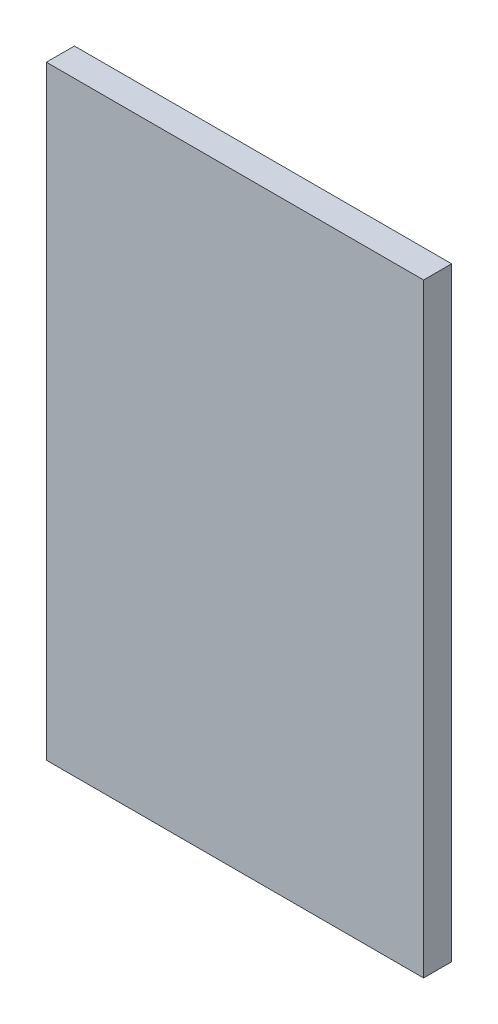
SolidWorks part; units mm, degrees
ref_plane "Front Plane" through (0, 0, 0) normal (0, 0, 1) x (1, 0, 0)
ref_plane "Top Plane" through (0, 0, 0) normal (0, 1, 0) x (1, 0, 0)
ref_plane "Right Plane" through (0, 0, 0) normal (1, 0, 0) x (0, 0, -1)
sketch "Sketch1" plane through (0, 0, 0) normal (0, 0, 1) x (1, 0, 0)
  line L0 (-39, -62.5) -> (39, 62.5) construction
  line L1 (-39, -62.5) -> (39, -62.5)
  line L2 (-39, -62.5) -> (-39, 62.5)
  line L3 (-39, 62.5) -> (39, 62.5)
  line L4 (39, -62.5) -> (39, 62.5)
  point P4 (0, -62.5)
  dimension "D1" = 125
  dimension "D2" = 78
extrude "Boss-Extrude1" add sketch "Sketch1" against normal blind 5.8 contours L1 L4 L3 L2
